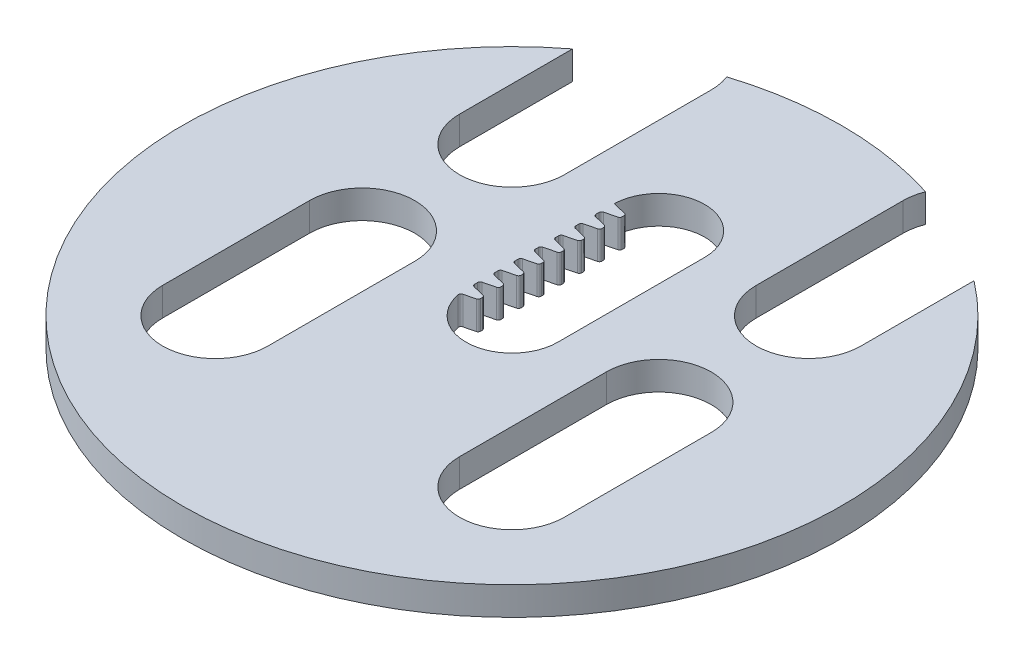
SolidWorks part; units mm, degrees
ref_plane "Front Plane" through (0, 0, 0) normal (0, 0, 1) x (1, 0, 0)
ref_plane "Top Plane" through (0, 0, 0) normal (0, 1, 0) x (1, 0, 0)
ref_plane "Right Plane" through (0, 0, 0) normal (1, 0, 0) x (0, 0, -1)
sketch "Sketch3" plane through (0, 0, 0) normal (0, -1, 0) x (1, 0, 0)
  line L0 (0, 0) -> (0, -17.78) construction
  line L1 (5.5562, 0) -> (5.5563, -17.78)
  line L2 (-5.5562, 0) -> (-5.5562, -17.78)
  line L3 (-17.9605, -35.7405) -> (17.9605, 0.1805) construction
  line L4 (-17.9605, 0.1805) -> (17.9605, -35.7405) construction
  line L5 (-17.9605, 0.1805) -> (17.9605, 0.1805) construction
  line L6 (-17.9605, 0.1805) -> (-17.9605, 17.9605) construction
  line L7 (-24.3305, 0.1805) -> (-24.3305, 17.9605)
  line L8 (-11.5905, 0.1805) -> (-11.5905, 17.9605)
  line L9 (-17.9605, -35.7405) -> (-17.9605, -17.9605) construction
  line L10 (-24.3105, -35.7405) -> (-24.3105, -17.9605)
  line L11 (-11.6105, -35.7405) -> (-11.6105, -17.9605)
  line L12 (17.9605, 0.1805) -> (17.9605, 17.9605) construction
  line L13 (11.6105, 0.1805) -> (11.6105, 17.9605)
  line L14 (24.3105, 0.1805) -> (24.3105, 17.9605)
  line L15 (17.9605, -35.7405) -> (17.9605, -17.9605) construction
  line L16 (11.6105, -35.7405) -> (11.6105, -17.9605)
  line L17 (24.3105, -35.7405) -> (24.3105, -17.9605)
  circle A0 centre (0, 0) radius 39.9034
  arc A1 (5.5562, 0) -> (-5.5562, 0) centre (0, 0) ccw
  arc A2 (-5.5562, -17.78) -> (5.5563, -17.78) centre (0, -17.78) ccw
  arc A3 (-24.3305, 0.1805) -> (-11.5905, 0.1805) centre (-17.9605, 0.1805) ccw
  arc A4 (-11.5905, 17.9605) -> (-24.3305, 17.9605) centre (-17.9605, 17.9605) ccw
  arc A5 (-24.3105, -35.7405) -> (-11.6105, -35.7405) centre (-17.9605, -35.7405) ccw
  arc A6 (-11.6105, -17.9605) -> (-24.3105, -17.9605) centre (-17.9605, -17.9605) ccw
  arc A7 (11.6105, 0.1805) -> (24.3105, 0.1805) centre (17.9605, 0.1805) ccw
  arc A8 (24.3105, 17.9605) -> (11.6105, 17.9605) centre (17.9605, 17.9605) ccw
  arc A9 (11.6105, -35.7405) -> (24.3105, -35.7405) centre (17.9605, -35.7405) ccw
  arc A10 (24.3105, -17.9605) -> (11.6105, -17.9605) centre (17.9605, -17.9605) ccw
  point P5 (0, -8.89)
  point P10 (-17.9605, 9.0705)
  point P13 (0, -17.78)
  point P16 (0, -17.78)
  point P22 (-17.9605, -26.8505)
  point P28 (17.9605, 9.0705)
  point P34 (17.9605, -26.8505)
  dimension "D1" = 79.8068
  dimension "D3" = 5.5562
  dimension "D8" = 6.37
  dimension "D10" = 6.35
  dimension "D13" = 6.35
  dimension "D14" = 6.35
  dimension "D2" = 17.78
  dimension "D4" = 45
  dimension "D5" = 45
  dimension "D6" = 50.8
extrude "Boss-Extrude1" add sketch "Sketch3" along normal blind 3.175 and the other way blind 0.254 contours L17 A10 L16 A0 L11 A6 L10 L2 A2 L1 A1 L8 A4 L7 A3 L14 A8 L13 A7
sketch "Sketch4" plane through (0, 0.254, 0) normal (0, 1, 0) x (1, 0, 0)
  line L0 (-5.5562, 0) -> (-3.6962, 0) construction
  line L1 (-3.6962, -0.34) -> (-3.6962, 0.34)
  line L2 (-3.6962, 0.34) -> (-5.5562, 0.8038)
  line L3 (-5.5562, 0) -> (-5.5562, 17.78) construction
  line L8 (-5.5562, 0.8038) -> (-5.5562, -0.8038)
  line L9 (-5.5562, -0.8038) -> (-3.6962, -0.34)
  point P7 (-3.6962, 0)
  dimension "D3" = 76
  dimension "D1" = 1.86
  dimension "D2" = 0.34
extrude "Boss-Extrude2" add sketch "Sketch4" against normal up to surface (3.429 mm away) up to face at (0, -3.175, -8.89)
pattern_linear "LPattern1" count 8 spacing 2.45 along (0, 0, -1) of "Boss-Extrude2"
fillet "Fillet1" radius 0.3 31 edges at (-3.6962, -1.4605, 0.34) (-5.5563, -1.4605, -1.6462) (-3.6962, -1.4605, -2.11) (-3.6962, -1.4605, -2.79) (-5.5562, -1.4605, -3.2538) (-5.5562, -1.4605, -4.0962) (-3.6962, -1.4605, -4.56) (-3.6962, -1.4605, -5.24) (-5.5562, -1.4605, -5.7038) (-5.5562, -1.4605, -6.5462) (-3.6962, -1.4605, -7.01) (-3.6962, -1.4605, -7.69) (-5.5562, -1.4605, -8.1538) (-5.5562, -1.4605, -8.9962) (-3.6962, -1.4605, -9.46) (-3.6962, -1.4605, -10.14) (-5.5562, -1.4605, -10.6038) (-5.5562, -1.4605, -11.4462) (-3.6962, -1.4605, -11.91) (-3.6962, -1.4605, -12.59) (-5.5562, -1.4605, -13.0538) (-5.5562, -1.4605, -13.8962) (-3.6962, -1.4605, -14.36) (-3.6962, -1.4605, -15.04) (-5.5562, -1.4605, -15.5038) (-5.5562, -1.4605, -16.3462) (-3.6962, -1.4605, -16.81) (-3.6962, -1.4605, -17.49) (-5.4998, -1.4605, 0.7897) (-5.5563, -1.4605, -0.8038) (-3.6962, -1.4605, -0.34)
equation "\"AIRFRAME_OD\"= 3.142in"
equation "\"AIRFRAME_ID\"= 3.00in"
equation "\"FLAT_T\"= 0.125in"
equation "\"COUPLER_OD\"= 2.998in"
equation "\"COUPLER_ID\"= 2.875in"
equation "\"NOSE_EXP_L\"= 3.5in"
equation "\"NOSE_SHOULDER_L\"= 1.5in"
equation "\"MAIN_L\"= 30in"
equation "\"RECO_COUP_L\"= 6in"
equation "\"RECO_SWITCH_L\"= 1.5in"
equation "\"RECO_ROD_X\"= 1.5in"
equation "\"DROGUE_L\"= 14in"
equation "\"ATS_FORE_COUP_L\"= 4in"
equation "\"ATS_AFT_COUP_L\"= 2.5in"
equation "\"ATS_ROD_X\"= 2in"
equation "\"LOWER_L\"= 16in"
equation "\"FIN_ROOT\"= 5in"
equation "\"FIN_X\"= 0.75in"
equation "\"FIN_N\"= 4"
equation "\"MOTOR_OD\"= 2.25in"
equation "\"MOTOR_ID\"= 2.126in"
equation "\"MOTOR_L\"= 8in"
equation "\"MOTOR_LOWER_X\"= 0.5in"
equation "\"CR_AFT_X\"= 0.5in"
equation "\"CR_FORE_X\"= 6in"
equation "\"D1@Boss-Extrude1\"=\"FLAT_T\""
equation "\"D1@Sketch3\"=\"AIRFRAME_OD\""
equation "\"D6@Sketch3\"=\"ATS_ROD_X\""
